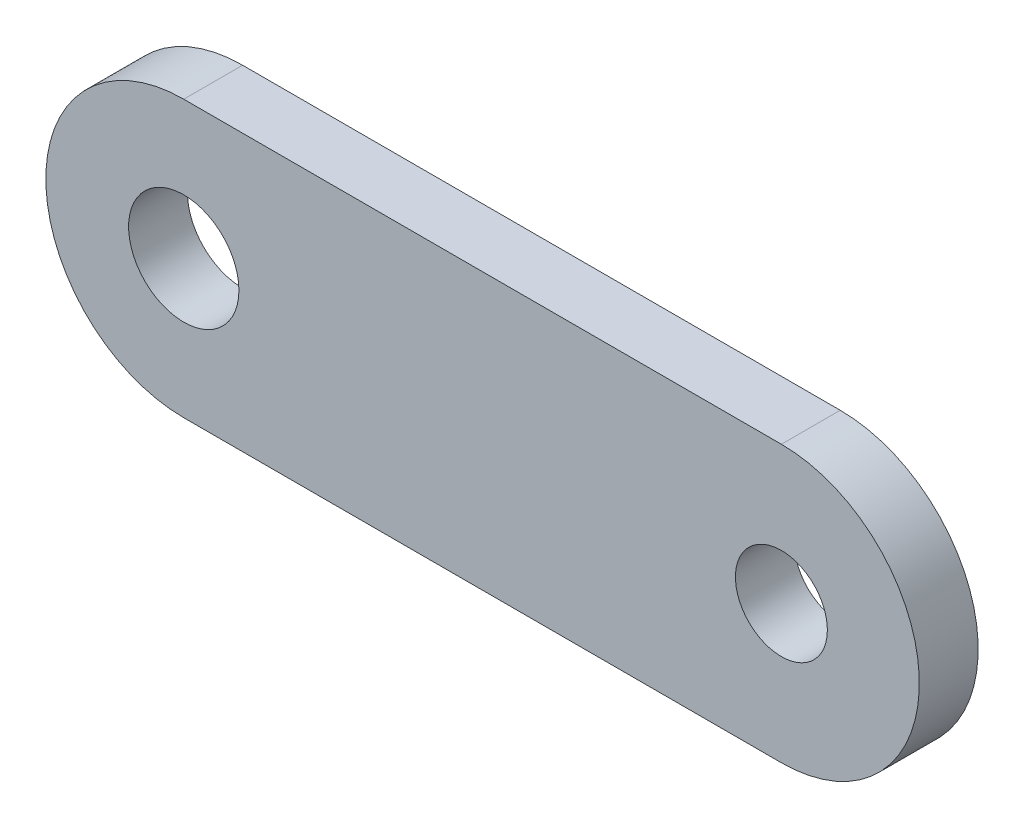
SolidWorks part; units mm, degrees
material "ABS"
ref_plane "Front Plane" through (0, 0, 0) normal (0, 0, 1) x (1, 0, 0)
ref_plane "Top Plane" through (0, 0, 0) normal (0, 1, 0) x (1, 0, 0)
ref_plane "Right Plane" through (0, 0, 0) normal (1, 0, 0) x (0, 0, -1)
sketch "Sketch1" plane through (0, 0, 0) normal (0, 0, 1) x (1, 0, 0)
  line L0 (-71.74, -4.7625) -> (-92.375, -4.7625)
  line L1 (-92.375, 4.7625) -> (-71.74, 4.7625)
  circle A0 centre (-71.74, 0) radius 1.5875
  circle A1 centre (-92.375, 0) radius 1.905
  arc A2 (-71.74, -4.7625) -> (-71.74, 4.7625) centre (-71.74, 0) ccw
  arc A3 (-92.375, 4.7625) -> (-92.375, -4.7625) centre (-92.375, 0) ccw
  dimension "D1" = 3.175
  dimension "D2" = 3.81
  dimension "D3" = 9.525
  dimension "D4" = 20.635
extrude "Boss-Extrude1" add sketch "Sketch1" along normal mid plane 2.032
